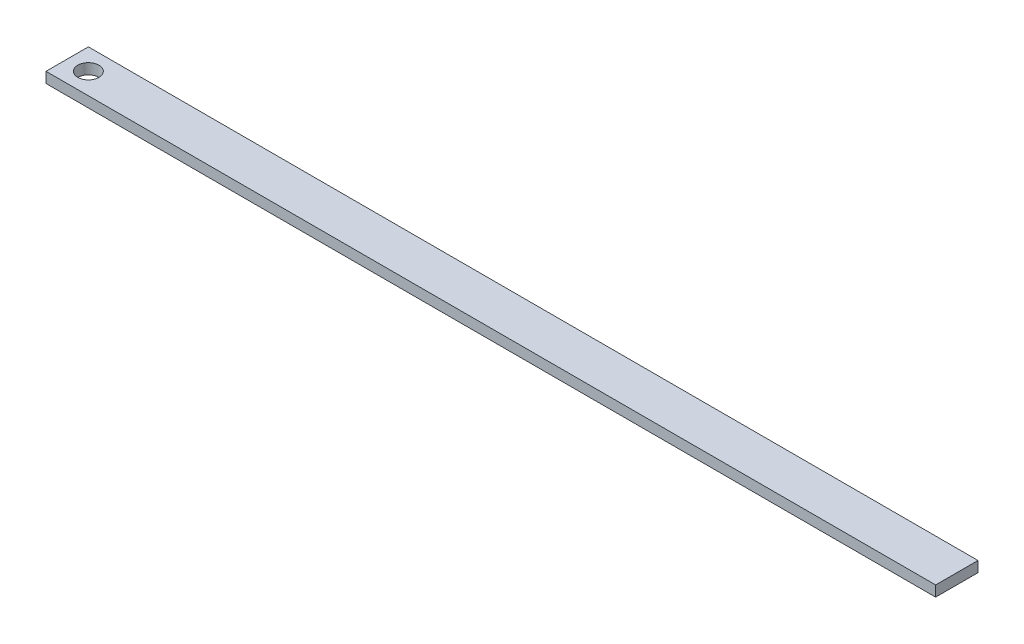
SolidWorks part; units mm, degrees
ref_plane "Front Plane" through (0, 0, 0) normal (0, 0, 1) x (1, 0, 0)
ref_plane "Top Plane" through (0, 0, 0) normal (0, 1, 0) x (1, 0, 0)
ref_plane "Right Plane" through (0, 0, 0) normal (1, 0, 0) x (0, 0, -1)
other "Configuration Table"
sketch "Contact_body_sketch" plane through (0, 0, 0) normal (0, 1, 0) x (1, 0, 0)
  line L0 (-10.5, 0) -> (10.5, 0) construction
  line L1 (-10.5, 0.5) -> (10.5, 0.5)
  line L2 (-10.5, 0.5) -> (-10.5, -0.5)
  line L3 (-10.5, -0.5) -> (10.5, -0.5)
  line L4 (10.5, 0.5) -> (10.5, -0.5)
  line L5 (-10.5, 0.5) -> (10.5, -0.5) construction
  line L6 (-10.5, -0.5) -> (10.5, 0.5) construction
  circle A0 centre (-10, 0) radius 0.25
  point P0 (0, 0)
  dimension "D3" = 0.5
  dimension "D1" = 21
  dimension "D2" = 1
  dimension "D4" = 0.5
extrude "Contact_body" add sketch "Contact_body_sketch" along normal blind 0.25
